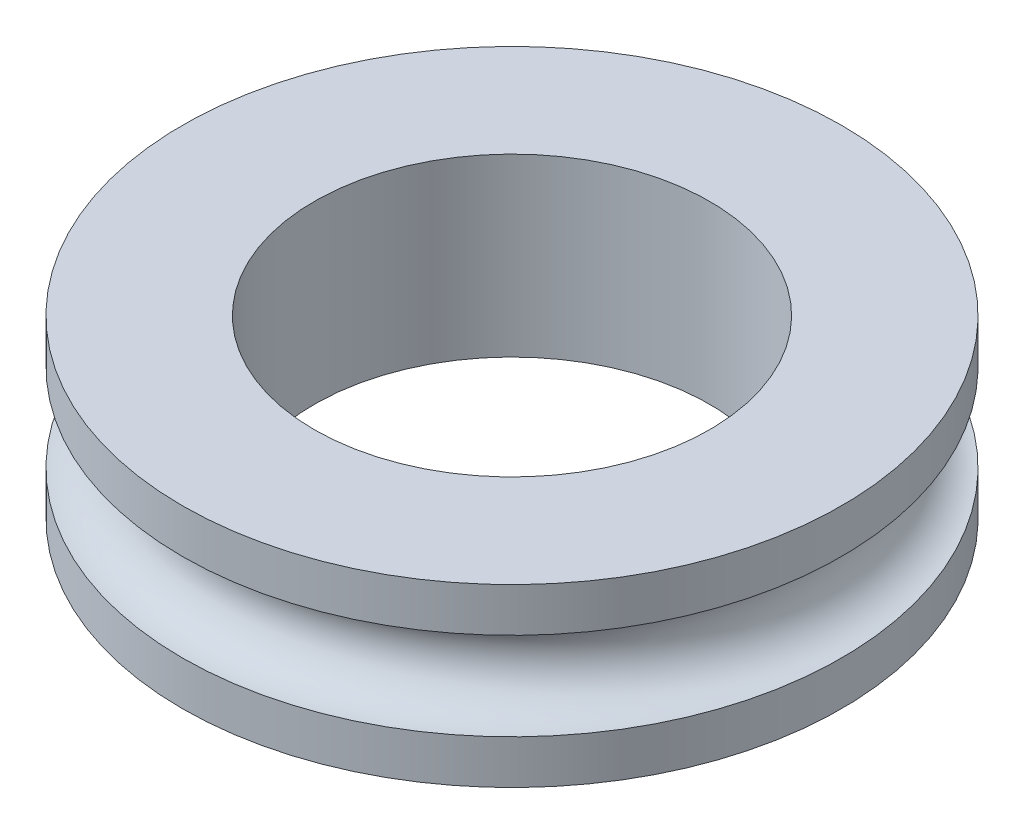
SolidWorks part; units mm, degrees
ref_plane "Front Plane" through (0, 0, 0) normal (0, 0, 1) x (1, 0, 0)
ref_plane "Top Plane" through (0, 0, 0) normal (0, 1, 0) x (1, 0, 0)
ref_plane "Right Plane" through (0, 0, 0) normal (1, 0, 0) x (0, 0, -1)
sketch "Sketch1" plane through (0, 0, 0) normal (0, 1, 0) x (1, 0, 0)
  circle A0 centre (0, 0) radius 7.5
  circle A1 centre (0, 0) radius 4.5
  dimension "D1" = 9
  dimension "D2" = 15
extrude "Boss-Extrude1" add sketch "Sketch1" along normal blind 4
ref_plane "Plane1" through (0, 2, 0) normal (0, 1, 0) x (1, 0, 0)
sketch "Sketch2" plane through (0, 2, 0) normal (0, 1, 0) x (1, 0, 0)
  circle A0 centre (0, 0) radius 6.5
  circle A3 centre (0, 0) radius 7.5 construction
  dimension "D1" = 1
sketch "Sketch3" plane through (0, 0, 0) normal (0, 0, 1) x (1, 0, 0)
  line L1 (-7.5, 4) -> (-7.5, 0) construction
  line L2 (-7.5, 1) -> (-7.5, 3)
  line L3 (0, 0) -> (0, 4) construction
  line L4 (7.5, 4) -> (-7.5, 4) construction
  line L5 (8.25, 2) -> (-8.25, 2) construction
  arc A1 (-7.5, 3) -> (-7.5, 1) centre (-7.5, 2) cw
  point P3 (-7.5, 4.1463)
  point P4 (0, 0)
  dimension "D1" = 2
revolve "Cut-Revolve1" cut sketch "Sketch3" angle 360 about L3
